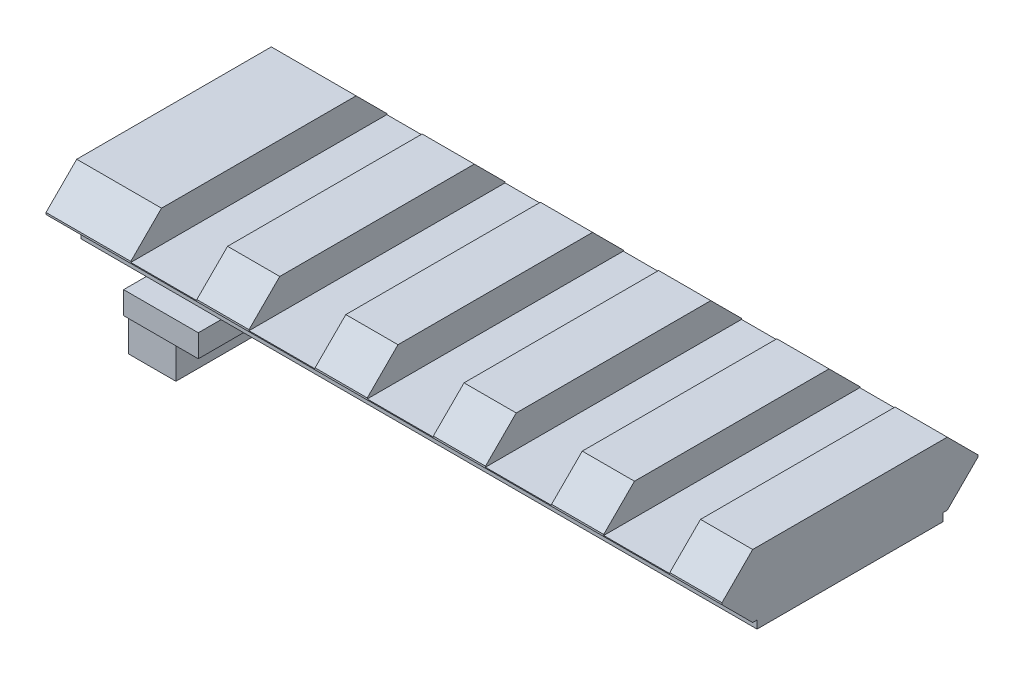
SolidWorks part; units mm, degrees
ref_plane "Front Plane" through (0, 0, 0) normal (0, 0, 1) x (1, 0, 0)
ref_plane "Top Plane" through (0, 0, 0) normal (0, 1, 0) x (1, 0, 0)
ref_plane "Right Plane" through (0, 0, 0) normal (1, 0, 0) x (0, 0, -1)
sketch "Sketch1" plane through (0, 0, 0) normal (1, 0, 0) x (0, 0, -1)
  line L10 (-7.8359, -6) -> (7.8359, -6)
  line L11 (7.8359, -6) -> (7.8359, -5.334)
  line L12 (7.8359, -5.334) -> (8.2042, -5.334)
  line L13 (8.2042, -5.334) -> (10.795, -2.7432)
  line L14 (10.795, -2.7432) -> (10.795, -2.5908)
  line L15 (10.795, -2.5908) -> (8.2042, 0)
  line L16 (8.2042, 0) -> (-8.2042, 0)
  line L17 (-8.2042, 0) -> (-10.795, -2.5908)
  line L18 (-10.795, -2.5908) -> (-10.795, -2.7432)
  line L19 (-10.795, -2.7432) -> (-8.2042, -5.334)
  line L20 (-8.2042, -5.334) -> (-7.8359, -5.334)
  line L21 (-7.8359, -5.334) -> (-7.8359, -6)
  line L22 (-9.4996, -1.2954) -> (-9.4996, -4.0386) construction
  line L23 (0, -995.7526) -> (0, 49004.2474) construction
  line L24 (-1007.0893, -1.2954) -> (48992.9107, -1.2954) construction
  line L25 (-1009.5011, -4.0386) -> (48990.4989, -4.0386) construction
  line L26 (-8.3457, -0.1415) -> (-35363.6848, -35355.4806) construction
  line L27 (-8.3711, -5.1671) -> (-35363.7101, 35350.1719) construction
  line L28 (8.3442, -0.14) -> (35363.6832, -35355.479) construction
  line L29 (8.3696, -5.1686) -> (35363.7086, 35350.1704) construction
  line L30 (9.4996, -1.2954) -> (9.4996, -4.0386) construction
  line L31 (-9.4996, -2.667) -> (9.4996, -2.667) construction
  point P18 (0, 0)
  dimension "D1" = 2.7432
  dimension "D2" = 18.9992
  dimension "D3" = 15.6718
  dimension "D4" = 6
  dimension "D5" = 4.0386
extrude "Boss-Extrude1" add sketch "Sketch1" along normal blind 57
sketch "Sketch2" plane through (0, 0, 0) normal (0, 1, 0) x (1, 0, 0)
  line L0 (57, 10.795) -> (0, 10.795) construction
  line L1 (47.03, 10.795) -> (52.6, 10.795)
  line L2 (47.03, 10.795) -> (47.03, -10.795)
  line L3 (47.03, -10.795) -> (52.6, -10.795)
  line L4 (52.6, 10.795) -> (52.6, -10.795)
  line L5 (57, -10.795) -> (0, -10.795) construction
  line L7 (57, 8.2042) -> (57, -8.2042) construction
  dimension "D1" = 5.57
  dimension "D2" = 4.4
ref_plane "Plane1" through (0, -2.667, 0) normal (0, 1, 0) x (1, 0, 0)
extrude "Cut-Extrude1" cut sketch "Sketch2" against normal up to surface (2.667 mm away) up to plane "Plane1"
pattern_linear "LPattern1" count 5 spacing 9.97 along (-1, 0, 0) of "Cut-Extrude1"
sketch "Sketch4" plane through (0, -6, 0) normal (0, -1, 0) x (1, 0, 0)
  line L0 (-1000, 0) -> (49000, 0) construction
  line L1 (5.5, -9.75) -> (11.8, -9.75)
  line L2 (5.5, -9.75) -> (5.5, 9.75)
  line L3 (5.5, 9.75) -> (11.8, 9.75)
  line L4 (11.8, -9.75) -> (11.8, 9.75)
  line L5 (0, 7.8359) -> (0, -7.8359) construction
  point P4 (5.5, 0)
  point P10 (0, 0)
  dimension "D1" = 6.3
  dimension "D2" = 19.5
  dimension "D3" = 5.5
extrude "Boss-Extrude3" add sketch "Sketch4" along normal blind 1.9
sketch "Sketch3" plane through (0, -7.9, 0) normal (0, -1, 0) x (1, 0, 0)
  line L0 (7.5, -9.34) -> (7.5, 9.34) construction
  line L1 (5.5, -9.34) -> (9.5, -9.34)
  line L2 (5.5, -9.34) -> (5.5, -0.99)
  line L3 (5.5, -0.99) -> (9.5, -0.99)
  line L4 (9.5, -9.34) -> (9.5, -0.99)
  line L5 (5.5, 1.99) -> (9.5, 1.99)
  line L6 (5.5, 1.99) -> (5.5, 9.34)
  line L7 (5.5, 9.34) -> (9.5, 9.34)
  line L8 (9.5, 1.99) -> (9.5, 9.34)
  line L11 (5.5, 9.75) -> (5.5, -9.75) construction
  line L12 (-1000, 0) -> (49000, 0) construction
  point P11 (7.5, 0)
  dimension "D1" = 8.35
  dimension "D2" = 4
  dimension "D3" = 7.35
  dimension "D4" = 4
  dimension "D5" = 2.98
extrude "Boss-Extrude2" add sketch "Sketch3" along normal blind 3
hole_wizard "Tap Drill for M2x0.4 Tap1" positions "Sketch5" profile "Sketch6" hole size "M2x0.4" standard "ANSI Metric"
sketch "Sketch5" plane through (0, -10.9, 0) normal (0, -1, 0) x (-1, 0, 0)
  line L0 (-7.5, -990.66) -> (-7.5, 49009.34) construction
  line L1 (-5.5, 9.34) -> (-9.5, 9.34) construction
  line L3 (-9.5, 0.99) -> (-5.5, 0.99) construction
  line L4 (-5.5, -1.99) -> (-9.5, -1.99) construction
  point P0 (-7.5, -6.24)
  point P2 (-7.5, 3.56)
  point P10 (-7.5, 9.34)
  dimension "D1" = 7.23
  dimension "D2" = 5.55
sketch "Sketch6" plane through (7.5, -10.9, 6.24) normal (1, 0, 0) x (0, 0, -1)
  line L0 (0, 0) -> (0, 5.7137)
  line L1 (0, 5.7137) -> (0.8, 5.233)
  line L2 (0.8, 5.233) -> (0.8, 0)
  line L5 (0.8, 0) -> (0, 0)
  line L10 (0, 5.7137) -> (-0.8, 5.233) construction
  line L11 (0, -6.35) -> (0, 107.95) construction
  dimension "Hole Dia." = 1.6
  dimension "Hole Depth" = 5.233
  dimension "Drill Angle" = 118
